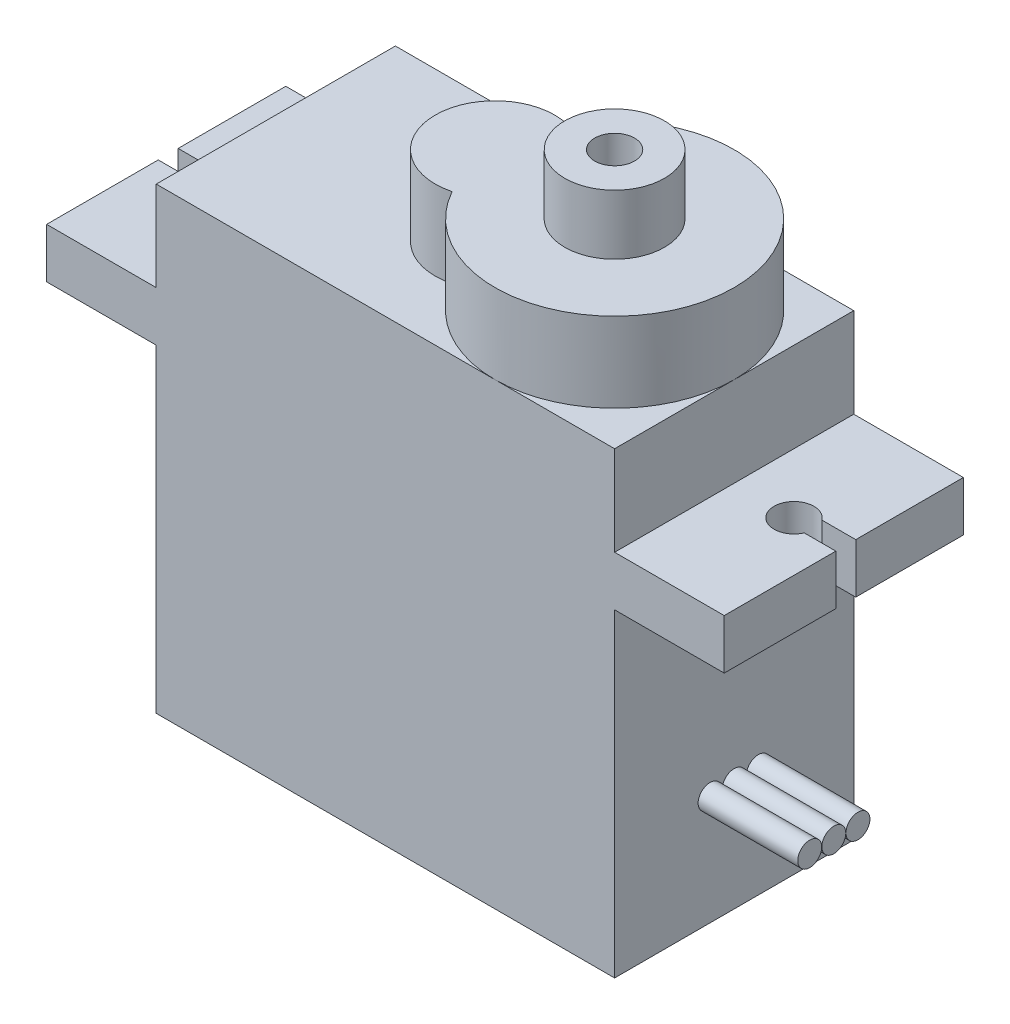
SolidWorks part; units mm, degrees
material "Rubber"
ref_plane "Front Plane" through (0, 0, 0) normal (0, 0, 1) x (1, 0, 0)
ref_plane "Top Plane" through (0, 0, 0) normal (0, 1, 0) x (1, 0, 0)
ref_plane "Right Plane" through (0, 0, 0) normal (1, 0, 0) x (0, 0, -1)
sketch "Sketch1" plane through (0, 0, 0) normal (0, 1, 0) x (1, 0, 0)
  line L1 (-11.5, -6) -> (11.5, -6)
  line L2 (-11.5, -6) -> (-11.5, 6)
  line L3 (-11.5, 6) -> (11.5, 6)
  line L4 (11.5, -6) -> (11.5, 6)
  line L5 (-11.5, -6) -> (11.5, 6) construction
  line L6 (-11.5, 6) -> (11.5, -6) construction
  point P0 (0, 0)
  dimension "D1" = 12
  dimension "D2" = 23
extrude "Boss-Extrude1" add sketch "Sketch1" along normal blind 23
sketch "Sketch2" plane through (-11.5, 0, 0) normal (-1, 0, 0) x (0, 0, 1)
  line L0 (-6, 23) -> (-6, 0) construction
  line L1 (-6, 18.5) -> (6, 18.5)
  line L2 (-6, 18.5) -> (-6, 16)
  line L3 (-6, 16) -> (6, 16)
  line L4 (6, 18.5) -> (6, 16)
  line L5 (6, 23) -> (6, 0) construction
  line L6 (-6, 0) -> (6, 0) construction
  dimension "D1" = 16
  dimension "D2" = 2.5
extrude "Boss-Extrude2" add sketch "Sketch2" along normal blind 5.5
sketch "Sketch3" plane through (0, 18.5, 0) normal (0, 1, 0) x (1, 0, 0)
  line L0 (-17, -6) -> (-17, 6) construction
  line L1 (-17, 0.6) -> (-15.3, 0.6)
  line L2 (-17, 0.6) -> (-17, -0.4)
  line L4 (-17, -0.4) -> (-15.4165, -0.4)
  line L6 (-11.5, -6) -> (-11.5, 6) construction
  arc A0 (-15.4165, -0.4) -> (-15.3, 0.6) centre (-14.5, 0) ccw
  point P10 (-11.5, 0)
  dimension "D1" = 2.5
  dimension "D2" = 2
  dimension "D3" = 1
extrude "Cut-Extrude1" cut sketch "Sketch3" against normal blind 5
mirror "Mirror1" about plane through (0, 0, 0) normal (1, 0, 0) of "Cut-Extrude1", "Boss-Extrude2"
sketch "Sketch4" plane through (0, 23, 0) normal (0, 1, 0) x (1, 0, 0)
  line L1 (11.5, -6) -> (11.5, 6) construction
  arc A0 (0.25, -2.9047) -> (0.25, 2.9047) centre (5.5, 0) ccw
  arc A1 (0.25, 2.9047) -> (0.25, -2.9047) centre (-0.5, 0) ccw
  dimension "D1" = 12
  dimension "D3" = 6
  dimension "D4" = 6
  dimension "D2" = 6
extrude "Boss-Extrude3" add sketch "Sketch4" along normal blind 4
sketch "Sketch5" plane through (0, 27, 0) normal (0, 1, 0) x (1, 0, 0)
  circle A0 centre (5.5, 0) radius 2.5
  circle A1 centre (5.5, 0) radius 6 construction
  circle A2 centre (5.5, 0) radius 1
  dimension "D1" = 0
  dimension "D2" = 5
  dimension "D3" = 2
extrude "Boss-Extrude4" add sketch "Sketch5" along normal blind 3
sketch "Sketch7" plane through (11.5, 0, 0) normal (1, 0, 0) x (0, 0, -1)
  circle A0 centre (0, 5.5) radius 0.6
  circle A1 centre (1.21, 5.5) radius 0.6
  circle A2 centre (-1.21, 5.5) radius 0.6
  dimension "D1" = 1.2
  dimension "D2" = 1.2
  dimension "D3" = 1.2
  dimension "D4" = 10.5
  dimension "D5" = 1.21
  dimension "D6" = 1.21
extrude "Boss-Extrude8" add sketch "Sketch7" along normal blind 5
